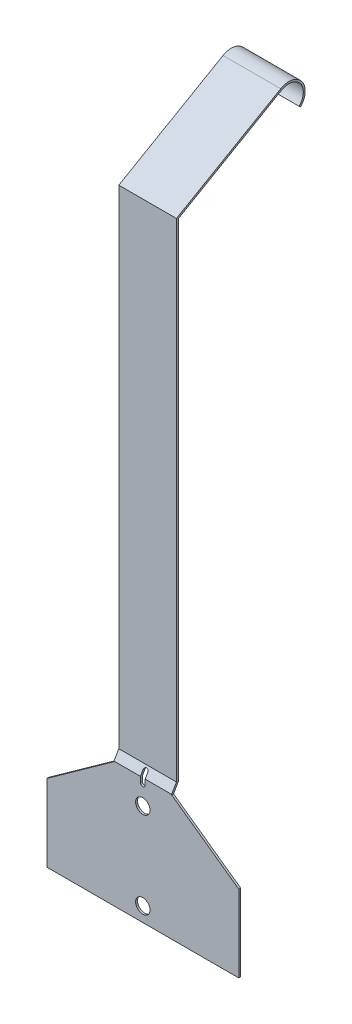
SolidWorks part; units mm, degrees
material "1060 Alloy"
ref_plane "Front" through (0, 0, 0) normal (0, 0, 1) x (1, 0, 0)
ref_plane "Top" through (0, 0, 0) normal (0, 1, 0) x (1, 0, 0)
ref_plane "Right" through (0, 0, 0) normal (1, 0, 0) x (0, 0, -1)
sketch "Sketch1" plane through (0, 0, 0) normal (1, 0, 0) x (0, 0, -1)
  line L0 (0, 0) -> (0, 165.1)
  line L1 (0, 165.1) -> (6.35, 176.0985)
  line L2 (6.35, 176.0985) -> (6.35, 820.325)
  line L3 (6.35, 820.325) -> (142.875, 899.1478)
  line L4 (152.4, 882.65) -> (177.3947, 882.65) construction
  arc A1 (142.875, 899.1478) -> (165.8704, 869.1796) centre (152.4, 882.65) cw
  dimension "D5" = 19.05
  dimension "D1" = 165.1
  dimension "D2" = 60
  dimension "D3" = 6.35
  dimension "D4" = 30
  dimension "D6" = 152.4
  dimension "D7" = 45
  dimension "D8" = 901.7
extrude "Extrude-Thin1" add sketch "Sketch1" along normal mid plane 76.2 thin wall 2.54
sketch "Sketch5" plane through (0, 0, 0) normal (0, 0, -1) x (-1, 0, 0)
  line L0 (126.873, 0) -> (-126.873, 0)
  line L1 (-126.873, 0) -> (-126.873, 101.6)
  line L2 (-126.873, 101.6) -> (-38.1, 165.1)
  line L3 (-38.1, 165.1) -> (38.1, 165.1)
  line L4 (38.1, 165.1) -> (126.873, 101.6)
  line L5 (126.873, 101.6) -> (126.873, 0)
  point P0 (0, 0)
  point P3 (0, 0)
  point P11 (0, 0)
  dimension "D1" = 253.746
  dimension "D2" = 101.6
extrude "Boss-Extrude1" add sketch "Sketch5" against normal blind 2.54
hole_wizard "3/4 (0.75) Diameter Hole1" positions "Sketch2" profile "Sketch3" hole size "3/4" standard "ANSI Inch" end condition through all
sketch "Sketch2" plane through (0, 0, 0) normal (0, 0, -1) x (-1, 0, 0)
  point P0 (0, 19.05)
  point P4 (0, 133.35)
  dimension "D1" = 19.05
  dimension "D2" = 114.3
sketch "Sketch3" plane through (0, 19.05, 0) normal (1, 0, 0) x (0, 1, 0)
  line L0 (0, 0) -> (0, 2.54)
  line L1 (0, 2.54) -> (9.525, 2.54)
  line L2 (9.525, 2.54) -> (9.525, 0)
  line L5 (9.525, 0) -> (0, 0)
  line L11 (0, -6.35) -> (0, 107.95) construction
  dimension "Thru Hole Dia." = 19.05
  dimension "Thru Hole Depth" = 2.54
sketch "Sketch4" plane through (0, 0, 2.54) normal (0, 0, 1) x (1, 0, 0)
  line L1 (0, 158.75) -> (0, 171.45) construction
  line L2 (-3.175, 158.75) -> (-3.175, 171.45)
  line L3 (3.175, 158.75) -> (3.175, 171.45)
  arc A2 (-3.175, 158.75) -> (3.175, 158.75) centre (0, 158.75) ccw
  arc A3 (3.175, 171.45) -> (-3.175, 171.45) centre (0, 171.45) ccw
  circle A4 centre (0, 133.35) radius 9.525 construction
  point P2 (0, 165.1)
  dimension "D1" = 6.35
  dimension "D2" = 12.7
  dimension "D3" = 25.4
extrude "Cut-Extrude1" cut sketch "Sketch4" against normal through all
